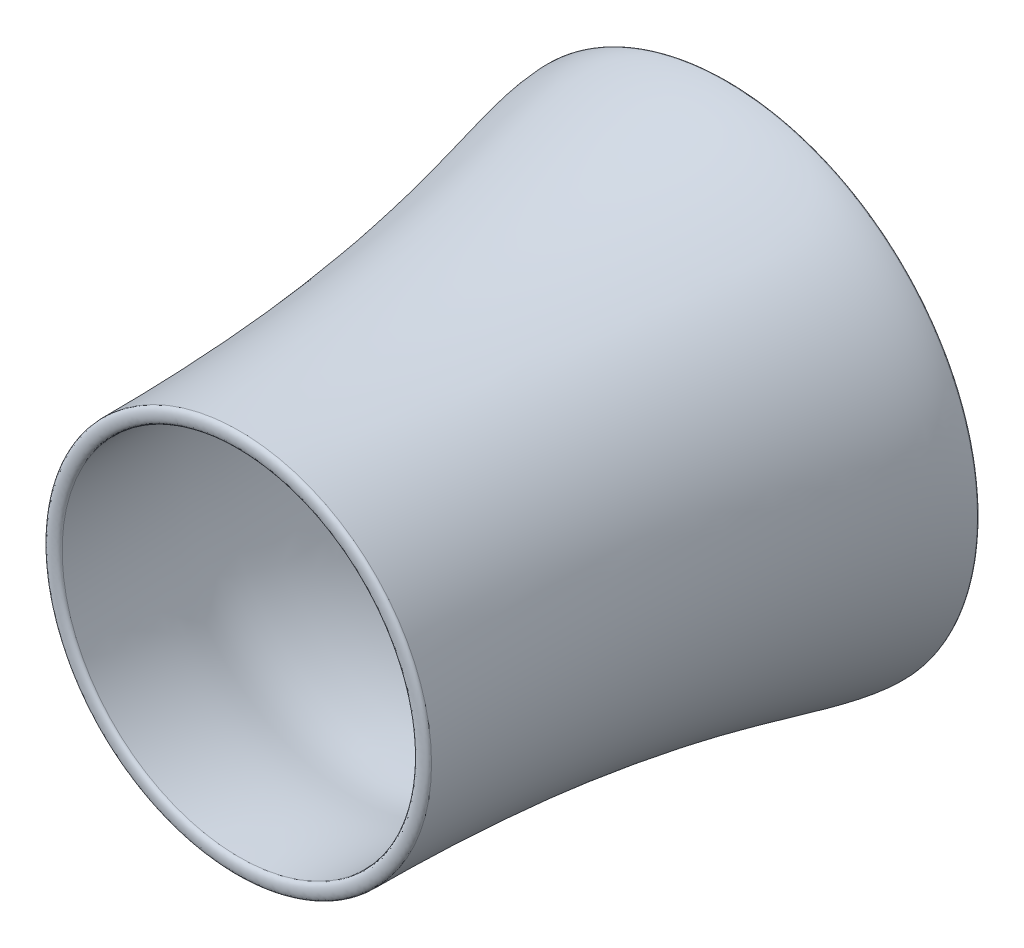
SolidWorks part; units mm, degrees
ref_plane "Front Plane" through (0, 0, 0) normal (0, 0, 1) x (1, 0, 0)
ref_plane "Top Plane" through (0, 0, 0) normal (0, 1, 0) x (1, 0, 0)
ref_plane "Right Plane" through (0, 0, 0) normal (1, 0, 0) x (0, 0, -1)
sketch "Sketch1" plane through (0, 0, 0) normal (0, 0, 1) x (1, 0, 0)
  circle A0 centre (0, 0) radius 50.8
  dimension "D1" = 101.6
ref_plane "Plane1" through (0, -254, 0) normal (0, 1, 0) x (1, 0, 0)
sketch "Sketch6" plane through (0, 0, 0) normal (0, 1, 0) x (1, 0, 0)
  line L0 (0, -99.6848) -> (0, 145.6048) construction
ref_plane "Plane2" through (0, -114.3, 0) normal (0, 1, 0) x (1, 0, 0)
sketch "Sketch12" plane through (0, 0, 0) normal (0, 1, 0) x (1, 0, 0)
  line L0 (0, -1104.7568) -> (0, -908.6135) construction
ref_plane "Plane3" through (0, 0, 203.2) normal (0, 0, 1) x (1, 0, 0)
ref_plane "Plane4" through (0, 0, 889) normal (0, 0, 1) x (1, 0, 0)
sketch "Sketch17" plane through (0, 0, 0) normal (0, 1, 0) x (1, 0, 0)
  line L0 (-259.4955, -43.5301) -> (-259.4955, 70.1436) construction
  line L1 (-110.6437, -1316.1124) -> (-110.6437, -853.5386) construction
  line L2 (-259.4955, 45.4622) -> (-387.328, 45.4622)
  line L3 (-387.328, 45.4622) -> (-387.328, -1084.8928)
  line L4 (-387.328, -1084.8928) -> (-110.6437, -1084.8928)
  spline S0 degree 3 poles (-259.4955, 45.4622) (-259.4955, -7.1736) (-207.7477, -105.8122) (-173.3147, -383.1384) (-92.4228, -818.9689) (-110.6437, -795.7842) (-110.6437, -1084.8928) knots 0 0 0 0 0.158009 0.206507 0.484977 1 1 1 1
sketch "Sketch21" plane through (0, 0, 0) normal (0, 1, 0) x (1, 0, 0)
  line L0 (-589.0994, -22.8536) -> (-589.0994, 113.778) construction
  line L1 (-450.1433, -1315.9117) -> (-450.1433, -853.874) construction
  line L2 (-422.1998, -32.2439) -> (-589.0994, -32.2439) construction
  line L3 (-415.0469, -1171.93) -> (-450.1433, -1171.93) construction
  line L4 (-415.0469, -1171.93) -> (-450.1433, -1171.93)
  line L6 (-422.1998, -32.2439) -> (-589.0994, -32.2439)
  spline S0 degree 3 poles (-422.1998, -32.2439) (-422.1998, -84.8797) (-496.283, -391.3247) (-428.7198, -617.1137) (-443.4861, -959.8391) (-415.0469, -882.8214) (-415.0469, -1171.93) knots 0 0 0 0 0.158009 0.206507 0.484977 1 1 1 1
  spline S1 degree 3 poles (-589.0994, -32.2439) (-589.0994, -157.6279) (-450.1433, -441.6209) (-450.1433, -1171.93) knots 0 0 0 0 1 1 1 1
  point P10 (-434.1212, -122.8466)
  point P11 (-417.4312, -771.3709)
  point P12 (-512.8024, -318.3576)
  point P13 (-434.1212, -814.2879)
  point P14 (-415.0469, -1171.93)
  point P15 (-422.1998, -48.9339)
  point P16 (-589.0994, -32.2439)
  point P17 (-472.2696, -463.7987)
revolve "Revolve2" add sketch "Sketch21" angle 360 about L0
sketch "Sketch22" plane through (0, 0, 0) normal (0, 1, 0) x (1, 0, 0)
  line L0 (-589.0994, -32.2439) -> (-422.1998, -32.2439)
  line L1 (-422.1998, -36.053) -> (-422.1998, -28.4349) construction
  line L2 (-589.0994, -30.8512) -> (-589.0994, -33.6367) construction
  spline S0 degree 3 poles (-589.0994, -32.2439) (-589.0994, -15.3106) (-422.1998, -15.3106) (-422.1998, -32.2439) knots 0 0 0 0 1 1 1 1
revolve "Revolve3" add sketch "Sketch22" angle 360 about L0
sketch "Sketch23" plane through (0, 0, 0) normal (0, 1, 0) x (1, 0, 0)
  line L0 (-450.1433, -1171.93) -> (-415.0469, -1171.93)
  line L1 (-450.1433, -1181.1411) -> (-450.1433, -1162.7189) construction
  line L2 (-415.0469, -1161.357) -> (-415.0469, -1182.503) construction
  spline S0 degree 3 poles (-450.1433, -1171.93) (-450.1433, -1184.63) (-415.0469, -1184.63) (-415.0469, -1171.93) knots 0 0 0 0 1 1 1 1
revolve "Revolve4" add sketch "Sketch23" angle 360 about L0
ref_plane "Plane5" through (289.9098, 0, 0) normal (1, 0, 0) x (0, 0, -1)
sketch "Sketch24" plane through (289.9098, 0, 0) normal (1, 0, 0) x (0, 0, -1)
  line L0 (-1123.5724, -17.6357) -> (119.2276, -17.6357) construction
  line L1 (-1171.93, 0) -> (-32.2439, 0) construction
  line L2 (-1171.93, -450.1433) -> (-1171.93, 450.1433) construction
  line L3 (-32.2439, 589.0994) -> (-32.2439, -589.0994) construction
  text T0 "MD-130 Gas Turbine Engine" font "TI-Nspire" height in points 160
